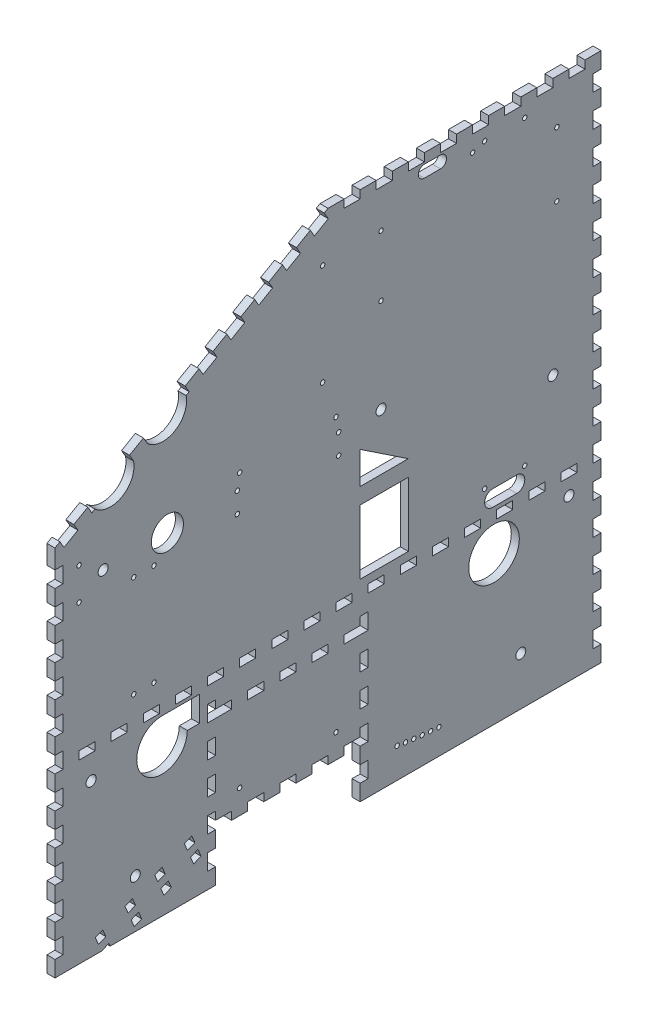
SolidWorks part; units mm, degrees
material "Pine"
ref_plane "Front Plane" through (0, 0, 0) normal (0, 0, 1) x (1, 0, 0)
ref_plane "Top Plane" through (0, 0, 0) normal (0, 1, 0) x (1, 0, 0)
ref_plane "Right Plane" through (0, 0, 0) normal (1, 0, 0) x (0, 0, -1)
sketch "Sketch2" plane through (0, 0, 0) normal (1, 0, 0) x (0, 0, -1)
  line L0 (0, 0) -> (0, 294.4501)
  line L1 (0, 294.4501) -> (215.9, 419.1)
  line L2 (215.9, 419.1) -> (431.8, 419.1)
  line L3 (431.8, 419.1) -> (431.8, 0)
  line L4 (431.8, 0) -> (241.3, 0)
  line L5 (241.3, 0) -> (241.3, 38.1)
  line L6 (241.3, 38.1) -> (127, 38.1)
  line L7 (127, 38.1) -> (127, 0)
  line L8 (127, 0) -> (0, 0)
  dimension "D1" = 431.8
  dimension "D2" = 419.1
  dimension "D3" = 127
  dimension "D4" = 114.3
  dimension "D5" = 38.1
  dimension "D6" = 215.9
  dimension "D7" = 150
extrude "Boss-Extrude1" add sketch "Sketch2" along normal blind 6.35 contours L1 L2 L3 L4 L5 L6 L7 L8 L0
sketch "Sketch3" plane through (6.35, 0, 0) normal (1, 0, 0) x (0, 0, -1)
  line L0 (0, 38.1) -> (431.8, 38.1) construction
  line L1 (0, 0) -> (0, 294.4501) construction
  line L2 (431.8, 419.1) -> (431.8, 0) construction
  circle A0 centre (63.5, 38.1) radius 3.9687
  circle A1 centre (368.3, 38.1) radius 3.9688
  dimension "D4" = 7.9375
  dimension "D5" = 7.9375
  dimension "D1" = 38.1
  dimension "D2" = 63.5
  dimension "D3" = 63.5
extrude "Cut-Extrude1" cut sketch "Sketch3" against normal through all
sketch "Sketch4" plane through (6.35, 0, 0) normal (1, 0, 0) x (0, 0, -1)
  line L0 (431.8, 419.1) -> (431.8, 0) construction
  line L1 (215.9, 419.1) -> (431.8, 419.1) construction
  line L2 (393.7, 400.05) -> (393.7, 19.05) construction
  line L4 (393.7, 400.05) -> (330.2, 400.05) construction
  line L5 (330.2, 400.05) -> (330.2, 19.05) construction
  line L6 (330.2, 400.05) -> (330.2, 19.05) construction
  line L7 (330.2, 400.05) -> (323.5506, 19.108) construction
  circle A0 centre (393.7, 400.05) radius 1.75 construction
  circle A1 centre (393.7, 19.05) radius 1.75 construction
  circle A2 centre (323.5506, 19.108) radius 1.75 construction
  circle A3 centre (316.9033, 19.2821) radius 1.75 construction
  circle A4 centre (330.2, 400.05) radius 1.75
  circle A5 centre (330.2, 19.05) radius 1.75 construction
  circle A6 centre (310.26, 19.5721) radius 1.75 construction
  circle A7 centre (303.6228, 19.9781) radius 1.75
  circle A8 centre (296.9937, 20.4998) radius 1.75
  circle A9 centre (290.3747, 21.1372) radius 1.75
  circle A10 centre (283.7678, 21.8899) radius 1.75
  circle A11 centre (277.175, 22.7579) radius 1.75
  circle A12 centre (270.5985, 23.7407) radius 1.75
  dimension "D1" = 3.5
  dimension "D2" = 38.1
  dimension "D3" = 19.05
  dimension "D4" = 381
  dimension "D5" = 10
  dimension "D6" = 1
  dimension "D7" = 101.6
extrude "Cut-Extrude2" cut sketch "Sketch4" against normal through all
sketch "Sketch5" plane through (6.35, 0, 0) normal (1, 0, 0) x (0, 0, -1)
  line L0 (431.8, 419.1) -> (431.8, 0) construction
  line L1 (431.8, 12.7) -> (425.45, 12.7)
  line L2 (431.8, 12.7) -> (431.8, 25.4)
  line L3 (431.8, 25.4) -> (425.45, 25.4)
  line L4 (425.45, 12.7) -> (425.45, 25.4)
  line L5 (431.8, 0) -> (241.3, 0) construction
  dimension "D1" = 6.35
  dimension "D2" = 12.7
  dimension "D3" = 12.7
extrude "Cut-Extrude3" cut sketch "Sketch5" against normal through all
pattern_linear "LPattern1" count 16 spacing 25.4 along (0, 1, 0) of "Cut-Extrude3"
sketch "Sketch6" plane through (6.35, 0, 0) normal (1, 0, 0) x (0, 0, -1)
  line L0 (0, 0) -> (0, 294.4501) construction
  line L1 (0, 12.7) -> (6.35, 12.7)
  line L2 (0, 12.7) -> (0, 25.4)
  line L3 (0, 25.4) -> (6.35, 25.4)
  line L4 (6.35, 12.7) -> (6.35, 25.4)
  line L5 (425.45, 12.7) -> (431.8, 12.7) construction
  line L6 (425.45, 25.4) -> (425.45, 12.7) construction
  line L7 (127, 0) -> (0, 0) construction
  dimension "D1" = 12.7
extrude "Cut-Extrude4" cut sketch "Sketch6" against normal through all
pattern_linear "LPattern2" count 11 spacing 25.4 along (0, 1, 0) of "Cut-Extrude4"
sketch "Sketch7" plane through (6.35, 0, 0) normal (1, 0, 0) x (0, 0, -1)
  line L0 (127, 38.1) -> (127, 0) construction
  line L1 (127, 12.7) -> (120.65, 12.7)
  line L2 (127, 12.7) -> (127, 25.4)
  line L3 (127, 25.4) -> (120.65, 25.4)
  line L4 (120.65, 12.7) -> (120.65, 25.4)
  line L5 (241.3, 38.1) -> (127, 38.1) construction
  line L6 (127, 38.1) -> (139.7, 38.1)
  line L7 (127, 38.1) -> (127, 44.45)
  line L8 (127, 44.45) -> (139.7, 44.45)
  line L9 (139.7, 38.1) -> (139.7, 44.45)
  line L10 (241.3, 0) -> (241.3, 38.1) construction
  line L11 (152.4, 38.1) -> (165.1, 38.1)
  line L12 (152.4, 38.1) -> (152.4, 44.45)
  line L13 (152.4, 44.45) -> (165.1, 44.45)
  line L14 (165.1, 38.1) -> (165.1, 44.45)
  line L15 (177.8, 38.1) -> (190.5, 38.1)
  line L16 (177.8, 38.1) -> (177.8, 44.45)
  line L17 (177.8, 44.45) -> (190.5, 44.45)
  line L18 (190.5, 38.1) -> (190.5, 44.45)
  line L19 (241.3, 25.4) -> (247.65, 25.4)
  line L20 (241.3, 25.4) -> (241.3, 12.7)
  line L21 (241.3, 12.7) -> (247.65, 12.7)
  line L22 (247.65, 25.4) -> (247.65, 12.7)
  line L23 (0, 12.7) -> (6.35, 12.7) construction
  line L24 (6.35, 12.7) -> (6.35, 25.4) construction
  line L25 (127, 0) -> (0, 0) construction
  line L26 (431.8, 0) -> (241.3, 0) construction
  line L27 (203.2, 44.45) -> (215.9, 44.45)
  line L28 (203.2, 44.45) -> (203.2, 38.1)
  line L29 (203.2, 38.1) -> (215.9, 38.1)
  line L30 (215.9, 44.45) -> (215.9, 38.1)
  line L32 (241.3, 38.1) -> (228.6, 38.1)
  line L33 (241.3, 38.1) -> (241.3, 44.45)
  line L34 (241.3, 44.45) -> (228.6, 44.45)
  line L35 (228.6, 38.1) -> (228.6, 44.45)
  dimension "D1" = 12.7
  dimension "D2" = 12.7
  dimension "D4" = 12.7
  dimension "D5" = 12.7
  dimension "D6" = 12.7
extrude "Cut-Extrude5" cut sketch "Sketch7" against normal through all
sketch "Sketch8" plane through (6.35, 0, 0) normal (1, 0, 0) x (0, 0, -1)
  line L0 (201.9351, 411.0373) -> (212.9336, 417.3873)
  line L1 (201.9351, 411.0373) -> (205.1101, 405.5381)
  line L2 (212.9336, 417.3873) -> (216.1086, 411.8881)
  line L3 (205.1101, 405.5381) -> (216.1086, 411.8881)
  line L4 (0, 294.4501) -> (215.9, 419.1) construction
  line L5 (6.35, 279.4) -> (0, 279.4) construction
  line L6 (6.35, 266.7) -> (6.35, 279.4) construction
  line L7 (216.1086, 411.8881) -> (7.1367, 291.2381) construction
  line L8 (6.35, 279.4) -> (6.35, 292.1) construction
  line L9 (215.9, 412.75) -> (215.6832, 412.6248) construction
  line L10 (7.1367, 291.2381) -> (3.9617, 296.7373) construction
  line L11 (6.35, 292.1) -> (6.5668, 292.2252) construction
  line L12 (215.9, 419.1) -> (215.9, 412.75) construction
  line L13 (215.9, 419.1) -> (431.8, 419.1) construction
  dimension "D1" = 215.9
  dimension "D2" = 241.3
  dimension "D3" = 6.35
extrude "Cut-Extrude6" cut sketch "Sketch8" against normal through all
pattern_linear "LPattern3" count 10 spacing 25.4 along (0, -0.5, 0.866) of "Cut-Extrude6"
sketch "Sketch9" plane through (6.35, 0, 0) normal (1, 0, 0) x (0, 0, -1)
  line L0 (215.9, 419.1) -> (431.8, 419.1) construction
  line L1 (419.1, 419.1) -> (406.4, 419.1)
  line L2 (419.1, 419.1) -> (419.1, 412.75)
  line L3 (419.1, 412.75) -> (406.4, 412.75)
  line L4 (406.4, 419.1) -> (406.4, 412.75)
  line L5 (431.8, 406.4) -> (425.45, 406.4) construction
  line L6 (425.45, 406.4) -> (425.45, 393.7) construction
  line L7 (431.8, 419.1) -> (431.8, 406.4) construction
  dimension "D1" = 12.7
extrude "Cut-Extrude7" cut sketch "Sketch9" against normal through all
pattern_linear "LPattern4" count 8 spacing 25.4 along (0, 0, 1) of "Cut-Extrude7"
sketch "Sketch10" plane through (6.35, 0, 0) normal (1, 0, 0) x (0, 0, -1)
  line L0 (127, 0) -> (0, 0) construction
  line L1 (146.05, 273.05) -> (222.25, 273.05) construction
  line L2 (146.05, 273.05) -> (146.05, 57.15) construction
  line L3 (146.05, 57.15) -> (222.25, 57.15) construction
  line L4 (222.25, 273.05) -> (222.25, 57.15) construction
  line L5 (146.05, 273.05) -> (19.05, 273.05) construction
  line L6 (146.05, 273.05) -> (146.05, 247.65) construction
  line L7 (146.05, 247.65) -> (19.05, 247.65) construction
  line L8 (19.05, 273.05) -> (19.05, 247.65) construction
  line L9 (0, 254) -> (0, 266.7) construction
  line L10 (127, 44.45) -> (127, 25.4) construction
  line L11 (241.3, 25.4) -> (241.3, 44.45) construction
  line L12 (152.4, 38.1) -> (139.7, 38.1) construction
  circle A0 centre (222.25, 273.05) radius 1.75
  circle A1 centre (222.25, 57.15) radius 1.75
  circle A2 centre (146.05, 57.15) radius 1.75
  circle A3 centre (146.05, 273.05) radius 1.75
  circle A4 centre (19.05, 273.05) radius 1.75
  circle A5 centre (19.05, 247.65) radius 1.75
  circle A6 centre (146.05, 247.65) radius 1.75 construction
  dimension "D4" = 3.5
  dimension "D1" = 273.05
  dimension "D2" = 19.05
  dimension "D3" = 247.65
  dimension "D5" = 19.05
  dimension "D6" = 19.05
  dimension "D7" = 19.05
extrude "Cut-Extrude8" cut sketch "Sketch10" against normal through all
sketch "Sketch11" plane through (6.35, 0, 0) normal (1, 0, 0) x (0, 0, -1)
  line L0 (127, 0) -> (0, 0) construction
  line L1 (0, 254) -> (0, 266.7) construction
  line L5 (241.3, 0) -> (241.3, 12.7) construction
  line L6 (177.8, 38.1) -> (165.1, 38.1) construction
  line L7 (38.1, 260.35) -> (257.81, 260.35) construction
  line L8 (257.81, 260.35) -> (257.81, 129.54) construction
  circle A0 centre (38.1, 260.35) radius 3.9688
  circle A1 centre (257.81, 129.54) radius 3.9688 construction
  circle A2 centre (257.81, 260.35) radius 3.9688
  dimension "D3" = 7.9375
  dimension "D1" = 260.35
  dimension "D2" = 38.1
  dimension "D4" = 16.51
  dimension "D5" = 91.44
extrude "Cut-Extrude9" cut sketch "Sketch11" against normal through all
sketch "Sketch12" plane through (6.35, 0, 0) normal (1, 0, 0) x (0, 0, -1)
  line L0 (127, 50.8) -> (127, 38.1)
  line L1 (120.65, 25.4) -> (127, 25.4)
  line L2 (120.65, 25.4) -> (120.65, 12.7)
  line L3 (120.65, 12.7) -> (127, 12.7)
  line L4 (127, 25.4) -> (127, 12.7)
  line L5 (120.65, 50.8) -> (127, 50.8)
  line L6 (120.65, 50.8) -> (120.65, 38.1)
  line L7 (120.65, 38.1) -> (127, 38.1)
  line L8 (127, 76.2) -> (127, 63.5)
  line L9 (120.65, 76.2) -> (127, 76.2)
  line L10 (120.65, 76.2) -> (120.65, 63.5)
  line L11 (120.65, 63.5) -> (127, 63.5)
  line L12 (127, 101.6) -> (127, 88.9)
  line L13 (120.65, 101.6) -> (127, 101.6)
  line L14 (120.65, 101.6) -> (120.65, 88.9)
  line L15 (120.65, 88.9) -> (127, 88.9)
  line L16 (127, 127) -> (127, 114.3)
  line L17 (120.65, 127) -> (127, 127)
  line L18 (120.65, 127) -> (120.65, 114.3)
  line L19 (120.65, 114.3) -> (127, 114.3)
  line L20 (127, 152.4) -> (127, 139.7) construction
  line L21 (120.65, 152.4) -> (127, 152.4) construction
  line L22 (120.65, 152.4) -> (120.65, 139.7) construction
  line L23 (120.65, 139.7) -> (127, 139.7) construction
  line L24 (127, 177.8) -> (127, 165.1) construction
  line L25 (120.65, 177.8) -> (127, 177.8) construction
  line L26 (120.65, 177.8) -> (120.65, 165.1) construction
  line L27 (120.65, 165.1) -> (127, 165.1) construction
  dimension "D1" = 7
extrude "Cut-Extrude13" cut sketch "Sketch12" against normal through all
sketch "Sketch13" plane through (6.35, 0, 0) normal (1, 0, 0) x (0, 0, -1)
  line L1 (120.65, 25.4) -> (120.65, 12.7) construction
  line L2 (84.65, 117.2) -> (347.15, 117.2) construction
  line L3 (84.65, 117.2) -> (6.35, 117.2) construction
  line L4 (6.35, 114.3) -> (6.35, 127) construction
  line L5 (347.15, 117.2) -> (425.45, 117.2) construction
  line L6 (425.45, 127) -> (425.45, 114.3) construction
  circle A0 centre (84.65, 117.2) radius 20
  circle A1 centre (347.15, 117.2) radius 20
  dimension "D2" = 40
  dimension "D1" = 9.8
  dimension "D3" = 36
extrude "Cut-Extrude14" cut sketch "Sketch13" against normal through all
sketch "Sketch14" plane through (6.35, 0, 0) normal (1, 0, 0) x (0, 0, -1)
  line L0 (36.9572, 315.7873) -> (47.9558, 322.1373)
  line L1 (36.9572, 315.7873) -> (40.1322, 310.2881)
  line L2 (47.9558, 322.1373) -> (51.1308, 316.6381)
  line L3 (40.1322, 310.2881) -> (51.1308, 316.6381)
  line L4 (80.9513, 341.1873) -> (91.9498, 347.5373)
  line L5 (80.9513, 341.1873) -> (84.1263, 335.6881)
  line L6 (91.9498, 347.5373) -> (95.1248, 342.0381)
  line L7 (84.1263, 335.6881) -> (95.1248, 342.0381)
  line L8 (91.9498, 347.5373) -> (95.1248, 342.0381) construction
extrude "Cut-Extrude15" cut sketch "Sketch14" against normal through all
sketch "Sketch15" plane through (6.35, 0, 0) normal (1, 0, 0) x (0, 0, -1)
  line L0 (43.8866, 319.2853) -> (85.4558, 343.2853) construction
  line L1 (46.8439, 314.1631) -> (53.1939, 303.1646) construction
  line L3 (64.6712, 331.2853) -> (64.4535, 331.6623) construction
  line L4 (58.9543, 328.4873) -> (69.9528, 334.8373) construction
  line L5 (29.1337, 303.9381) -> (62.1293, 322.9881) construction
  line L6 (31.5586, 305.3381) -> (62.1293, 322.9881)
  line L7 (73.1278, 329.3381) -> (103.6985, 346.9881)
  line L8 (73.1278, 329.3381) -> (106.1234, 348.3881) construction
  circle A0 centre (43.8866, 319.2853) radius 18.6147
  circle A1 centre (85.4558, 343.2853) radius 18.6147
  dimension "D2" = 12.7
  dimension "D1" = 48
extrude "Cut-Extrude16" cut sketch "Sketch15" against normal through all contours L6 A0 | L7 A1
sketch "Sketch17" plane through (6.35, 0, 0) normal (1, 0, 0) x (0, 0, -1)
  line L0 (0, 139.7) -> (6.35, 139.7) construction
  line L1 (19.05, 146.05) -> (31.75, 146.05)
  line L2 (19.05, 146.05) -> (19.05, 139.7)
  line L3 (19.05, 139.7) -> (31.75, 139.7)
  line L4 (31.75, 146.05) -> (31.75, 139.7)
  line L5 (6.35, 139.7) -> (6.35, 152.4) construction
  dimension "D1" = 12.7
  dimension "D2" = 6.35
  dimension "D3" = 12.7
extrude "Cut-Extrude17" cut sketch "Sketch17" against normal through all
pattern_linear "LPattern5" count 17 spacing 25.4 along (0, 0, -1) of "Cut-Extrude17"
pattern_linear "LPattern6" count 2 spacing 120.65 along (0, 0, -1) of "Cut-Extrude13"
sketch "Sketch18" plane through (6.35, 0, 0) normal (1, 0, 0) x (0, 0, -1)
  line L1 (127, 120.65) -> (139.7, 120.65)
  line L2 (127, 120.65) -> (127, 114.3)
  line L3 (127, 114.3) -> (139.7, 114.3)
  line L4 (139.7, 120.65) -> (139.7, 114.3)
  dimension "D1" = 12.7
  dimension "D2" = 6.35
extrude "Cut-Extrude18" cut sketch "Sketch18" against normal through all
pattern_linear "LPattern7" count 5 spacing 25.4 along (0, 0, -1) of "Cut-Extrude18"
sketch "Sketch19" plane through (6.35, 0, 0) normal (1, 0, 0) x (0, 0, -1)
  line L0 (127, 0) -> (0, 0) construction
  line L1 (0, 101.6) -> (0, 114.3) construction
  circle A0 centre (28.575, 107.95) radius 4
  dimension "D3" = 8
  dimension "D1" = 107.95
  dimension "D2" = 28.575
extrude "Cut-Extrude19" cut sketch "Sketch19" against normal through all
sketch "Sketch20" plane through (6.35, 0, 0) normal (1, 0, 0) x (0, 0, -1)
  line L1 (292.1, 406.4) -> (304.8, 406.4) construction
  line L2 (292.1, 411.1625) -> (304.8, 411.1625)
  line L3 (292.1, 401.6375) -> (304.8, 401.6375)
  line L4 (304.8, 419.1) -> (304.8, 412.75) construction
  line L5 (292.1, 412.75) -> (292.1, 419.1) construction
  line L6 (279.4, 412.75) -> (292.1, 412.75) construction
  arc A0 (292.1, 411.1625) -> (292.1, 401.6375) centre (292.1, 406.4) ccw
  arc A2 (304.8, 401.6375) -> (304.8, 411.1625) centre (304.8, 406.4) ccw
  point P2 (298.45, 406.4)
  dimension "D1" = 9.525
  dimension "D2" = 6.35
extrude "Cut-Extrude20" cut sketch "Sketch20" against normal through all
sketch "Sketch22" plane through (6.35, 0, 0) normal (1, 0, 0) x (0, 0, -1)
  line L0 (120.65, 38.1) -> (28.6685, 0) construction
  line L1 (106.4867, 39.1066) -> (111.3468, 27.3733) construction
  line L2 (104.7684, 34.9582) -> (102.3384, 40.8249)
  line L3 (104.7684, 34.9582) -> (110.635, 37.3883)
  line L4 (102.3384, 40.8249) -> (108.205, 43.2549)
  line L5 (110.635, 37.3883) -> (108.205, 43.2549)
  line L6 (104.7684, 34.9582) -> (108.205, 43.2549) construction
  line L7 (102.3384, 40.8249) -> (110.635, 37.3883) construction
  line L8 (107.1984, 29.0916) -> (109.6285, 23.2249)
  line L9 (107.1984, 29.0916) -> (113.0651, 31.5216)
  line L10 (109.6285, 23.2249) -> (115.4951, 25.655)
  line L11 (113.0651, 31.5216) -> (115.4951, 25.655)
  line L12 (107.1984, 29.0916) -> (115.4951, 25.655) construction
  line L13 (109.6285, 23.2249) -> (113.0651, 31.5216) construction
  line L15 (127, 0) -> (0, 0) construction
  point P6 (108.9167, 33.2399)
  dimension "D1" = 6.35
  dimension "D2" = 12.7
  dimension "D3" = 6.35
  dimension "D4" = 22.5
extrude "Cut-Extrude22" cut sketch "Sketch22" against normal through all
pattern_linear "LPattern9" count 4 spacing 25.4 along (0, -0.3827, 0.9239) of "Cut-Extrude22"
pattern_linear "LPattern10" count 2 spacing 12.7 along (0, -1, 0) count 2 spacing 12.7 along (0, 1, 0) of "Cut-Extrude19"
sketch "Sketch23" plane through (6.35, 0, 0) normal (1, 0, 0) x (0, 0, -1)
  line L0 (38.1, 260.35) -> (88.9, 260.35) construction
  circle A0 centre (88.9, 260.35) radius 12.7
  dimension "D1" = 25.4
  dimension "D2" = 50.8
extrude "Cut-Extrude23" cut sketch "Sketch23" against normal through all
sketch "Sketch24" plane through (6.35, 0, 0) normal (1, 0, 0) x (0, 0, -1)
  line L0 (365.125, 155.575) -> (346.075, 155.575) construction
  line L1 (365.125, 149.225) -> (346.075, 149.225)
  line L2 (365.125, 161.925) -> (346.075, 161.925)
  line L3 (355.6, 155.575) -> (355.6, 139.7) construction
  line L5 (336.55, 146.05) -> (323.85, 146.05) construction
  line L6 (349.25, 139.7) -> (361.95, 139.7) construction
  arc A0 (365.125, 149.225) -> (365.125, 161.925) centre (365.125, 155.575) ccw
  arc A2 (346.075, 161.925) -> (346.075, 149.225) centre (346.075, 155.575) ccw
  point P2 (355.6, 155.575)
  dimension "D1" = 12.7
  dimension "D2" = 19.05
  dimension "D3" = 3.175
extrude "Cut-Extrude24" cut sketch "Sketch24" against normal through all
sketch "Sketch26" plane through (6.35, 0, 0) normal (1, 0, 0) x (0, 0, -1)
  line L1 (241.3, 152.4) -> (279.4, 152.4)
  line L2 (241.3, 152.4) -> (241.3, 203.2)
  line L3 (241.3, 203.2) -> (279.4, 203.2)
  line L4 (279.4, 152.4) -> (279.4, 203.2)
  line L5 (260.35, 146.05) -> (247.65, 146.05) construction
  line L6 (241.3, 101.6) -> (241.3, 88.9) construction
  dimension "D1" = 6.35
  dimension "D2" = 50.8
  dimension "D3" = 38.1
extrude "Cut-Extrude26" cut sketch "Sketch26" against normal through all
sketch "Sketch27" plane through (6.35, 0, 0) normal (1, 0, 0) x (0, 0, -1)
  line L0 (241.3, 215.9) -> (241.3, 241.3)
  line L1 (241.3, 241.3) -> (279.4, 215.9)
  line L2 (279.4, 215.9) -> (241.3, 215.9)
  line L3 (241.3, 203.2) -> (241.3, 152.4) construction
  line L4 (279.4, 152.4) -> (279.4, 203.2) construction
  line L5 (279.4, 203.2) -> (241.3, 203.2) construction
  dimension "D1" = 12.7
  dimension "D2" = 25.4
extrude "Cut-Extrude27" cut sketch "Sketch27" against normal through all
sketch "Sketch28" plane through (6.35, 0, 0) normal (1, 0, 0) x (0, 0, -1)
  line L1 (18.6517, 88.0539) -> (35.9159, 88.0539)
  line L2 (18.6517, 88.0539) -> (18.6517, 113.3314)
  line L3 (18.6517, 113.3314) -> (35.9159, 113.3314)
  line L4 (35.9159, 88.0539) -> (35.9159, 113.3314)
extrude "Boss-Extrude2" add sketch "Sketch28" against normal through all
sketch "Sketch29" plane through (6.35, 0, 0) normal (1, 0, 0) x (0, 0, -1)
  line L0 (120.65, 127) -> (120.65, 114.3) construction
  line L1 (114.3, 137.2) -> (84.65, 137.2)
  line L2 (114.3, 137.2) -> (114.3, 117.2)
  line L3 (114.3, 117.2) -> (84.65, 117.2)
  line L4 (84.65, 137.2) -> (84.65, 117.2)
  circle A0 centre (84.65, 117.2) radius 20 construction
  dimension "D1" = 6.35
extrude "Cut-Extrude28" cut sketch "Sketch29" against normal through all
sketch "Sketch30" plane through (0, 0, 0) normal (-1, 0, 0) x (0, 0, 1)
  line L0 (-361.95, 146.05) -> (-349.25, 146.05) construction
  line L1 (-371.475, 403.225) -> (-339.725, 403.225) construction
  line L2 (-371.475, 403.225) -> (-371.475, 165.1) construction
  line L3 (-371.475, 165.1) -> (-339.725, 165.1) construction
  line L4 (-339.725, 403.225) -> (-339.725, 165.1) construction
  line L6 (-355.6, 165.1) -> (-355.6, 139.7) construction
  line L7 (-349.25, 139.7) -> (-361.95, 139.7) construction
  circle A0 centre (-371.475, 165.1) radius 1.75
  circle A1 centre (-339.725, 165.1) radius 1.75
  circle A2 centre (-339.725, 403.225) radius 1.75
  circle A3 centre (-371.475, 403.225) radius 1.75
  dimension "D4" = 3.5
  dimension "D1" = 19.05
  dimension "D2" = 31.75
  dimension "D3" = 238.125
extrude "Cut-Extrude29" cut sketch "Sketch30" against normal through all
sketch "Sketch31" plane through (0, 0, 0) normal (-1, 0, 0) x (0, 0, 1)
  line L1 (-78.3, 243.25) -> (-62.3, 243.25) construction
  line L2 (-78.3, 243.25) -> (-78.3, 163.1114) construction
  line L3 (-78.3, 163.1114) -> (-62.3, 163.1114) construction
  line L4 (-62.3, 243.25) -> (-62.3, 163.1114) construction
  circle A0 centre (-78.3, 243.25) radius 2.425 construction
  circle A1 centre (-62.3, 163.1114) radius 2.425 construction
  circle A2 centre (-78.3, 243.25) radius 1.75
  circle A3 centre (-62.3, 243.25) radius 1.75
  circle A4 centre (-62.3, 163.1114) radius 1.75
  circle A5 centre (-78.3, 163.1114) radius 1.75
  circle A6 centre (-19.05, 247.65) radius 1.75 construction
extrude "Cut-Extrude30" cut sketch "Sketch31" against normal through all
sketch "Sketch32" plane through (0, 0, 0) normal (-1, 0, 0) x (0, 0, 1)
  line L0 (-211.65, 382.05) -> (-211.65, 301.9114) construction
  line L2 (-224.3386, 245.55) -> (-144.2, 245.55) construction
  line L3 (-224.3386, 245.55) -> (-224.3386, 261.55) construction
  line L4 (-224.3386, 261.55) -> (-144.2, 261.55) construction
  line L5 (-144.2, 245.55) -> (-144.2, 261.55) construction
  arc A0 (-214.075, 382.05) -> (-209.225, 382.05) centre (-211.65, 382.05) ccw construction
  arc A1 (-214.075, 301.9114) -> (-209.225, 301.9114) centre (-211.65, 301.9114) ccw construction
  circle A2 centre (-224.3386, 261.55) radius 2.425 construction
  circle A6 centre (-144.2, 245.55) radius 2.425 construction
  circle A7 centre (-211.65, 382.05) radius 1.75
  circle A8 centre (-211.65, 301.9114) radius 1.75
  circle A9 centre (-224.3386, 261.55) radius 1.75
  circle A10 centre (-224.3386, 245.55) radius 1.75
  circle A11 centre (-144.2, 261.55) radius 1.75
  circle A12 centre (-144.2, 245.55) radius 1.75
  circle A13 centre (-222.25, 273.05) radius 1.75 construction
extrude "Cut-Extrude31" cut sketch "Sketch32" against normal through all
sketch "Sketch33" plane through (0, 0, 0) normal (-1, 0, 0) x (0, 0, 1)
  line L0 (-396.875, 384.175) -> (-396.875, 333.375) construction
  line L1 (-257.825, 382.775) -> (-257.825, 334.775) construction
  circle A0 centre (-396.875, 384.175) radius 1.75 construction
  circle A1 centre (-396.875, 333.375) radius 1.75 construction
  circle A2 centre (-257.825, 382.775) radius 1.75 construction
  circle A3 centre (-257.825, 334.775) radius 1.75 construction
  circle A4 centre (-396.875, 384.175) radius 1.75
  circle A5 centre (-396.875, 333.375) radius 1.75
  circle A6 centre (-257.825, 334.775) radius 1.75
  circle A7 centre (-257.825, 382.775) radius 1.75
  circle A8 centre (-371.475, 403.225) radius 1.75 construction
extrude "Cut-Extrude32" cut sketch "Sketch33" against normal through all
sketch "Sketch34" plane through (0, 0, 0) normal (-1, 0, 0) x (0, 0, 1)
  line L2 (-431.8, 139.7) -> (-431.8, 127) construction
  line L3 (-431.8, 127) -> (-425.45, 127) construction
  circle A0 centre (-406.4, 127) radius 3.9688
  dimension "D3" = 7.9375
  dimension "D2" = 25.4
extrude "Cut-Extrude33" cut sketch "Sketch34" against normal through all
sketch "Sketch35" plane through (0, 0, 0) normal (-1, 0, 0) x (0, 0, 1)
  line L0 (-431.8, 0) -> (-241.3, 0) construction
  line L1 (-431.8, 215.9) -> (-431.8, 203.2) construction
  circle A0 centre (-393.7, 215.9) radius 3.9688
  dimension "D3" = 7.9375
  dimension "D1" = 215.9
  dimension "D2" = 38.1
extrude "Cut-Extrude34" cut sketch "Sketch35" against normal through all
